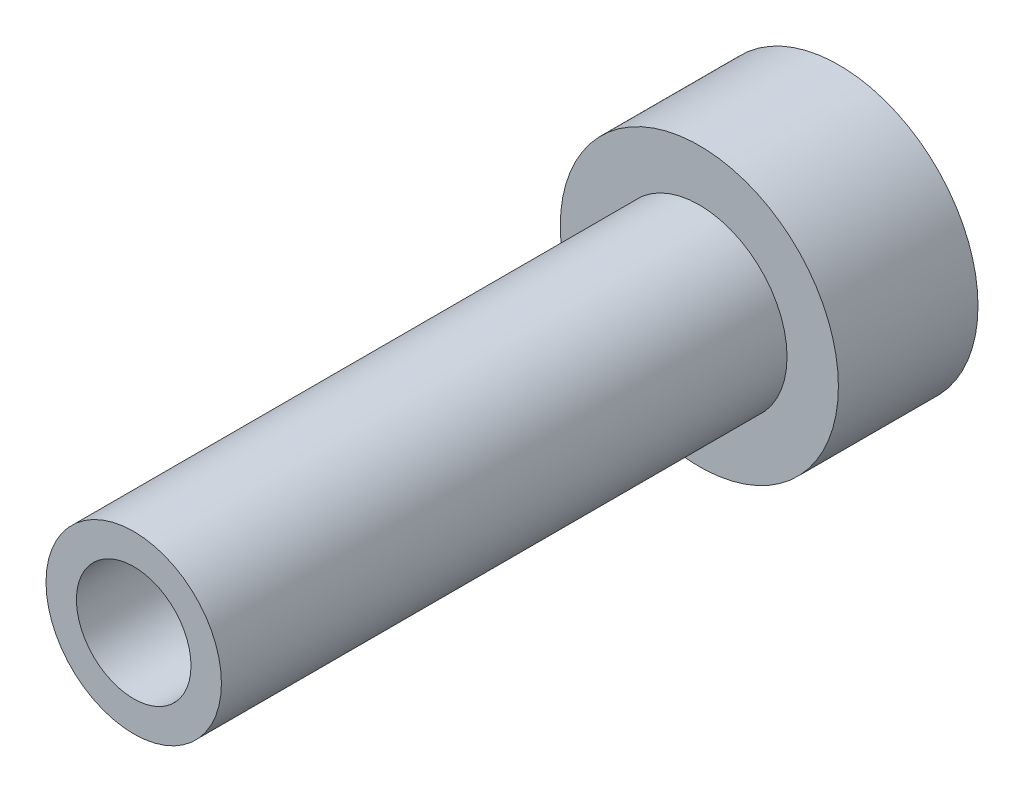
SolidWorks part; units mm, degrees
ref_plane "Front Plane" through (0, 0, 0) normal (0, 0, 1) x (1, 0, 0)
ref_plane "Top Plane" through (0, 0, 0) normal (0, 1, 0) x (1, 0, 0)
ref_plane "Right Plane" through (0, 0, 0) normal (1, 0, 0) x (0, 0, -1)
sketch "Sketch1" plane through (0, 0, 0) normal (0, 0, 1) x (1, 0, 0)
  line L264 (0.9685, 13.0819) -> (0.6041, 12.7214)
  line L265 (0.5718, 12.7289) -> (0.4042, 13.2133)
  line L266 (0.4042, 13.2133) -> (0.1146, 12.7903)
  line L267 (0.0815, 12.7916) -> (-0.1748, 13.2355)
  line L268 (-0.1748, 13.2355) -> (-0.379, 12.7653)
  line L269 (-0.4118, 12.7603) -> (-0.7474, 13.1477)
  line L270 (-0.7474, 13.1477) -> (-0.859, 12.6474)
  line L271 (-0.8902, 12.6363) -> (-1.2932, 12.9531)
  line L272 (-1.2932, 12.9531) -> (-1.308, 12.4408)
  line L273 (-1.3366, 12.4239) -> (-1.7922, 12.6588)
  line L274 (-1.7922, 12.6588) -> (-1.7098, 12.1529)
  line L275 (-1.7347, 12.1309) -> (-2.2265, 12.2753)
  line L276 (-2.2265, 12.2753) -> (-2.0499, 11.7941)
  line L277 (-2.0701, 11.7679) -> (-2.5804, 11.8166)
  line L278 (-2.5804, 11.8166) -> (-2.3159, 11.3775)
  line L279 (-2.3308, 11.3479) -> (-2.8411, 11.2992)
  line L280 (-2.8411, 11.2992) -> (-2.4983, 10.9181)
  line L281 (-2.5073, 10.8862) -> (-2.9991, 10.7418)
  line L282 (-2.9991, 10.7418) -> (-2.5904, 10.4325)
  line L283 (-2.5932, 10.3995) -> (-3.0488, 10.1646)
  line L284 (-3.0488, 10.1646) -> (-2.589, 9.9382)
  line L285 (-2.5855, 9.9052) -> (-2.9884, 9.5884)
  line L286 (-2.9884, 9.5884) -> (-2.494, 9.4531)
  line L287 (-2.4844, 9.4214) -> (-2.82, 9.034)
  line L288 (-2.82, 9.034) -> (-2.3089, 8.9948)
  line L289 (-2.2935, 8.9655) -> (-2.5497, 8.5215)
  line L290 (-2.5497, 8.5215) -> (-2.0405, 8.5797)
  line L291 (-2.0198, 8.5539) -> (-2.1874, 8.0695)
  line L292 (-2.1874, 8.0695) -> (-1.6983, 8.223)
  line L293 (-1.6731, 8.2015) -> (-1.746, 7.6942)
  line L294 (-1.746, 7.6942) -> (-1.2949, 7.9374)
  line L295 (-1.266, 7.9211) -> (-1.2416, 7.4092)
  line L296 (-1.2416, 7.4092) -> (-0.8446, 7.7334)
  line L297 (-0.8132, 7.7229) -> (-0.6924, 7.2248)
  line L298 (-0.6924, 7.2248) -> (-0.3639, 7.6183)
  line L299 (-0.3311, 7.6139) -> (-0.1182, 7.1477)
  line L300 (-0.1182, 7.1477) -> (0.1299, 7.5962)
  line L301 (0.1629, 7.5981) -> (0.4603, 7.1806)
  line L302 (0.4603, 7.1806) -> (0.6189, 7.668)
  line L303 (0.651, 7.6761) -> (1.022, 7.3224)
  line L304 (1.022, 7.3224) -> (1.0855, 7.831)
  line L305 (1.1155, 7.8451) -> (1.5468, 7.568)
  line L306 (1.5468, 7.568) -> (1.5129, 8.0794)
  line L307 (1.5397, 8.0989) -> (2.0155, 7.9084)
  line L308 (2.0155, 7.9084) -> (1.8855, 8.4042)
  line L309 (1.9081, 8.4284) -> (2.4114, 8.3314)
  line L310 (2.4114, 8.3314) -> (2.1899, 8.7936)
  line L311 (2.2076, 8.8217) -> (2.7201, 8.8217)
  line L312 (2.7201, 8.8217) -> (2.4151, 9.2337)
  line L313 (2.4271, 9.2645) -> (2.9304, 9.3616)
  line L314 (2.9304, 9.3616) -> (2.553, 9.7083)
  line L315 (2.559, 9.7409) -> (3.0348, 9.9314)
  line L316 (3.0348, 9.9314) -> (2.5985, 10.2005)
  line L317 (2.5982, 10.2336) -> (3.0294, 10.5108)
  line L318 (3.0294, 10.5108) -> (2.5501, 10.6924)
  line L319 (2.5435, 10.7249) -> (2.9145, 11.0786)
  line L320 (2.9145, 11.0786) -> (2.4095, 11.1663)
  line L321 (2.3969, 11.1969) -> (2.6941, 11.6145)
  line L322 (2.6941, 11.6145) -> (2.1817, 11.605)
  line L323 (2.1635, 11.6327) -> (2.3764, 12.0989)
  line L324 (2.3764, 12.0989) -> (1.875, 11.9926)
  line L325 (1.8519, 12.0164) -> (1.9727, 12.5145)
  line L326 (1.9727, 12.5145) -> (1.5005, 12.3152)
  line L327 (1.4733, 12.3342) -> (1.4977, 12.8462)
  line L328 (1.4977, 12.8462) -> (1.0717, 12.5611)
  line L329 (1.0414, 12.5746) -> (0.9685, 13.0819)
  line L330 (0.9685, 13.0819) -> (0.6041, 12.7214)
  line L331 (0.5718, 12.7289) -> (0.4042, 13.2133)
  line L332 (0.4042, 13.2133) -> (0.1146, 12.7903)
  line L333 (0.0815, 12.7916) -> (-0.1748, 13.2355)
  line L334 (-0.1748, 13.2355) -> (-0.379, 12.7653)
  line L335 (-0.4118, 12.7603) -> (-0.7474, 13.1477)
  line L336 (-0.7474, 13.1477) -> (-0.859, 12.6474)
  line L337 (-0.8902, 12.6363) -> (-1.2932, 12.9531)
  line L338 (-1.2932, 12.9531) -> (-1.308, 12.4408)
  line L339 (-1.3366, 12.4239) -> (-1.7922, 12.6588)
  line L340 (-1.7922, 12.6588) -> (-1.7098, 12.1529)
  line L341 (-1.7347, 12.1309) -> (-2.2265, 12.2753)
  line L342 (-2.2265, 12.2753) -> (-2.0499, 11.7941)
  line L343 (-2.0701, 11.7679) -> (-2.5804, 11.8166)
  line L344 (-2.5804, 11.8166) -> (-2.3159, 11.3775)
  line L345 (-2.3308, 11.3479) -> (-2.8411, 11.2992)
  line L346 (-2.8411, 11.2992) -> (-2.4983, 10.9181)
  line L347 (-2.5073, 10.8862) -> (-2.9991, 10.7418)
  line L348 (-2.9991, 10.7418) -> (-2.5904, 10.4325)
  line L349 (-2.5932, 10.3995) -> (-3.0488, 10.1646)
  line L350 (-3.0488, 10.1646) -> (-2.589, 9.9382)
  line L351 (-2.5855, 9.9052) -> (-2.9884, 9.5884)
  line L352 (-2.9884, 9.5884) -> (-2.494, 9.4531)
  line L353 (-2.4844, 9.4214) -> (-2.82, 9.034)
  line L354 (-2.82, 9.034) -> (-2.3089, 8.9948)
  line L355 (-2.2935, 8.9655) -> (-2.5497, 8.5215)
  line L356 (-2.5497, 8.5215) -> (-2.0405, 8.5797)
  line L357 (-2.0198, 8.5539) -> (-2.1874, 8.0695)
  line L358 (-2.1874, 8.0695) -> (-1.6983, 8.223)
  line L359 (-1.6731, 8.2015) -> (-1.746, 7.6942)
  line L360 (-1.746, 7.6942) -> (-1.2949, 7.9374)
  line L361 (-1.266, 7.9211) -> (-1.2416, 7.4092)
  line L362 (-1.2416, 7.4092) -> (-0.8446, 7.7334)
  line L363 (-0.8132, 7.7229) -> (-0.6924, 7.2248)
  line L364 (-0.6924, 7.2248) -> (-0.3639, 7.6183)
  line L365 (-0.3311, 7.6139) -> (-0.1182, 7.1477)
  line L366 (-0.1182, 7.1477) -> (0.1299, 7.5962)
  line L367 (0.1629, 7.5981) -> (0.4603, 7.1806)
  line L368 (0.4603, 7.1806) -> (0.6189, 7.668)
  line L369 (0.651, 7.6761) -> (1.022, 7.3224)
  line L370 (1.022, 7.3224) -> (1.0855, 7.831)
  line L371 (1.1155, 7.8451) -> (1.5468, 7.568)
  line L372 (1.5468, 7.568) -> (1.5129, 8.0794)
  line L373 (1.5397, 8.0989) -> (2.0155, 7.9084)
  line L374 (2.0155, 7.9084) -> (1.8855, 8.4042)
  line L375 (1.9081, 8.4284) -> (2.4114, 8.3314)
  line L376 (2.4114, 8.3314) -> (2.1899, 8.7936)
  line L377 (2.2076, 8.8217) -> (2.7201, 8.8217)
  line L378 (2.7201, 8.8217) -> (2.4151, 9.2337)
  line L379 (2.4271, 9.2645) -> (2.9304, 9.3616)
  line L380 (2.9304, 9.3616) -> (2.553, 9.7083)
  line L381 (2.559, 9.7409) -> (3.0348, 9.9314)
  line L382 (3.0348, 9.9314) -> (2.5985, 10.2005)
  line L383 (2.5982, 10.2336) -> (3.0294, 10.5108)
  line L384 (3.0294, 10.5108) -> (2.5501, 10.6924)
  line L385 (2.5435, 10.7249) -> (2.9145, 11.0786)
  line L386 (2.9145, 11.0786) -> (2.4095, 11.1663)
  line L387 (2.3969, 11.1969) -> (2.6941, 11.6145)
  line L388 (2.6941, 11.6145) -> (2.1817, 11.605)
  line L389 (2.1635, 11.6327) -> (2.3764, 12.0989)
  line L390 (2.3764, 12.0989) -> (1.875, 11.9926)
  line L391 (1.8519, 12.0164) -> (1.9727, 12.5145)
  line L392 (1.9727, 12.5145) -> (1.5005, 12.3152)
  line L393 (1.4733, 12.3342) -> (1.4977, 12.8462)
  line L394 (1.4977, 12.8462) -> (1.0717, 12.5611)
  line L395 (1.0414, 12.5746) -> (0.9685, 13.0819)
  circle A99 centre (-0.0015, 10.1929) radius 3.8845
  arc A132 (0.6041, 12.7214) -> (0.5718, 12.7289) centre (-0.0015, 10.1929) ccw
  arc A133 (0.1146, 12.7903) -> (0.0815, 12.7916) centre (-0.0015, 10.1929) ccw
  arc A134 (-0.379, 12.7653) -> (-0.4118, 12.7603) centre (-0.0015, 10.1929) ccw
  arc A135 (-0.859, 12.6474) -> (-0.8902, 12.6363) centre (-0.0015, 10.1929) ccw
  arc A136 (-1.308, 12.4408) -> (-1.3366, 12.4239) centre (-0.0015, 10.1929) ccw
  arc A137 (-1.7098, 12.1529) -> (-1.7347, 12.1309) centre (-0.0015, 10.1929) ccw
  arc A138 (-2.0499, 11.7941) -> (-2.0701, 11.7679) centre (-0.0015, 10.1929) ccw
  arc A139 (-2.3159, 11.3775) -> (-2.3308, 11.3479) centre (-0.0015, 10.1929) ccw
  arc A140 (-2.4983, 10.9181) -> (-2.5073, 10.8862) centre (-0.0015, 10.1929) ccw
  arc A141 (-2.5904, 10.4325) -> (-2.5932, 10.3995) centre (-0.0015, 10.1929) ccw
  arc A142 (-2.589, 9.9382) -> (-2.5855, 9.9052) centre (-0.0015, 10.1929) ccw
  arc A143 (-2.494, 9.4531) -> (-2.4844, 9.4214) centre (-0.0015, 10.1929) ccw
  arc A144 (-2.3089, 8.9948) -> (-2.2935, 8.9655) centre (-0.0015, 10.1929) ccw
  arc A145 (-2.0405, 8.5797) -> (-2.0198, 8.5539) centre (-0.0015, 10.1929) ccw
  arc A146 (-1.6983, 8.223) -> (-1.6731, 8.2015) centre (-0.0015, 10.1929) ccw
  arc A147 (-1.2949, 7.9374) -> (-1.266, 7.9211) centre (-0.0015, 10.1929) ccw
  arc A148 (-0.8446, 7.7334) -> (-0.8132, 7.7229) centre (-0.0015, 10.1929) ccw
  arc A149 (-0.3639, 7.6183) -> (-0.3311, 7.6139) centre (-0.0015, 10.1929) ccw
  arc A150 (0.1299, 7.5962) -> (0.1629, 7.5981) centre (-0.0015, 10.1929) ccw
  arc A151 (0.6189, 7.668) -> (0.651, 7.6761) centre (-0.0015, 10.1929) ccw
  arc A152 (1.0855, 7.831) -> (1.1155, 7.8451) centre (-0.0015, 10.1929) ccw
  arc A153 (1.5129, 8.0794) -> (1.5397, 8.0989) centre (-0.0015, 10.1929) ccw
  arc A154 (1.8855, 8.4042) -> (1.9081, 8.4284) centre (-0.0015, 10.1929) ccw
  arc A155 (2.1899, 8.7936) -> (2.2076, 8.8217) centre (-0.0015, 10.1929) ccw
  arc A156 (2.4151, 9.2337) -> (2.4271, 9.2645) centre (-0.0015, 10.1929) ccw
  arc A157 (2.553, 9.7083) -> (2.559, 9.7409) centre (-0.0015, 10.1929) ccw
  arc A158 (2.5985, 10.2005) -> (2.5982, 10.2336) centre (-0.0015, 10.1929) ccw
  arc A159 (2.5501, 10.6924) -> (2.5435, 10.7249) centre (-0.0015, 10.1929) ccw
  arc A160 (2.4095, 11.1663) -> (2.3969, 11.1969) centre (-0.0015, 10.1929) ccw
  arc A161 (2.1817, 11.605) -> (2.1635, 11.6327) centre (-0.0015, 10.1929) ccw
  arc A162 (1.875, 11.9926) -> (1.8519, 12.0164) centre (-0.0015, 10.1929) ccw
  arc A163 (1.5005, 12.3152) -> (1.4733, 12.3342) centre (-0.0015, 10.1929) ccw
  arc A164 (1.0717, 12.5611) -> (1.0414, 12.5746) centre (-0.0015, 10.1929) ccw
  arc A165 (0.6041, 12.7214) -> (0.5718, 12.7289) centre (-0.0015, 10.1929) ccw
  arc A166 (0.1146, 12.7903) -> (0.0815, 12.7916) centre (-0.0015, 10.1929) ccw
  arc A167 (-0.379, 12.7653) -> (-0.4118, 12.7603) centre (-0.0015, 10.1929) ccw
  arc A168 (-0.859, 12.6474) -> (-0.8902, 12.6363) centre (-0.0015, 10.1929) ccw
  arc A169 (-1.308, 12.4408) -> (-1.3366, 12.4239) centre (-0.0015, 10.1929) ccw
  arc A170 (-1.7098, 12.1529) -> (-1.7347, 12.1309) centre (-0.0015, 10.1929) ccw
  arc A171 (-2.0499, 11.7941) -> (-2.0701, 11.7679) centre (-0.0015, 10.1929) ccw
  arc A172 (-2.3159, 11.3775) -> (-2.3308, 11.3479) centre (-0.0015, 10.1929) ccw
  arc A173 (-2.4983, 10.9181) -> (-2.5073, 10.8862) centre (-0.0015, 10.1929) ccw
  arc A174 (-2.5904, 10.4325) -> (-2.5932, 10.3995) centre (-0.0015, 10.1929) ccw
  arc A175 (-2.589, 9.9382) -> (-2.5855, 9.9052) centre (-0.0015, 10.1929) ccw
  arc A176 (-2.494, 9.4531) -> (-2.4844, 9.4214) centre (-0.0015, 10.1929) ccw
  arc A177 (-2.3089, 8.9948) -> (-2.2935, 8.9655) centre (-0.0015, 10.1929) ccw
  arc A178 (-2.0405, 8.5797) -> (-2.0198, 8.5539) centre (-0.0015, 10.1929) ccw
  arc A179 (-1.6983, 8.223) -> (-1.6731, 8.2015) centre (-0.0015, 10.1929) ccw
  arc A180 (-1.2949, 7.9374) -> (-1.266, 7.9211) centre (-0.0015, 10.1929) ccw
  arc A181 (-0.8446, 7.7334) -> (-0.8132, 7.7229) centre (-0.0015, 10.1929) ccw
  arc A182 (-0.3639, 7.6183) -> (-0.3311, 7.6139) centre (-0.0015, 10.1929) ccw
  arc A183 (0.1299, 7.5962) -> (0.1629, 7.5981) centre (-0.0015, 10.1929) ccw
  arc A184 (0.6189, 7.668) -> (0.651, 7.6761) centre (-0.0015, 10.1929) ccw
  arc A185 (1.0855, 7.831) -> (1.1155, 7.8451) centre (-0.0015, 10.1929) ccw
  arc A186 (1.5129, 8.0794) -> (1.5397, 8.0989) centre (-0.0015, 10.1929) ccw
  arc A187 (1.8855, 8.4042) -> (1.9081, 8.4284) centre (-0.0015, 10.1929) ccw
  arc A188 (2.1899, 8.7936) -> (2.2076, 8.8217) centre (-0.0015, 10.1929) ccw
  arc A189 (2.4151, 9.2337) -> (2.4271, 9.2645) centre (-0.0015, 10.1929) ccw
  arc A190 (2.553, 9.7083) -> (2.559, 9.7409) centre (-0.0015, 10.1929) ccw
  arc A191 (2.5985, 10.2005) -> (2.5982, 10.2336) centre (-0.0015, 10.1929) ccw
  arc A192 (2.5501, 10.6924) -> (2.5435, 10.7249) centre (-0.0015, 10.1929) ccw
  arc A193 (2.4095, 11.1663) -> (2.3969, 11.1969) centre (-0.0015, 10.1929) ccw
  arc A194 (2.1817, 11.605) -> (2.1635, 11.6327) centre (-0.0015, 10.1929) ccw
  arc A195 (1.875, 11.9926) -> (1.8519, 12.0164) centre (-0.0015, 10.1929) ccw
  arc A196 (1.5005, 12.3152) -> (1.4733, 12.3342) centre (-0.0015, 10.1929) ccw
  arc A197 (1.0717, 12.5611) -> (1.0414, 12.5746) centre (-0.0015, 10.1929) ccw
  dimension "D1" = 0.1
extrude "Boss-Extrude1" add sketch "Sketch1" along normal up to surface (2.9 mm away) from offset 0.1
sketch "Sketch2" plane through (0, 0, 3) normal (0, 0, 1) x (1, 0, 0)
  circle A0 centre (-0.0015, 10.1929) radius 3.8845
  circle A1 centre (-0.0015, 10.1929) radius 1.6
  dimension "D1" = 3.2
extrude "Boss-Extrude2" add sketch "Sketch2" along normal blind 1
sketch "Sketch3" plane through (0, 0, 4) normal (0, 0, 1) x (1, 0, 0)
  circle A0 centre (-0.0015, 10.1929) radius 1.6
  circle A1 centre (-0.0015, 10.1929) radius 2.45
  dimension "D1" = 4.9
  dimension "D2" = 3.2
extrude "Boss-Extrude3" add sketch "Sketch3" along normal blind 15.8
